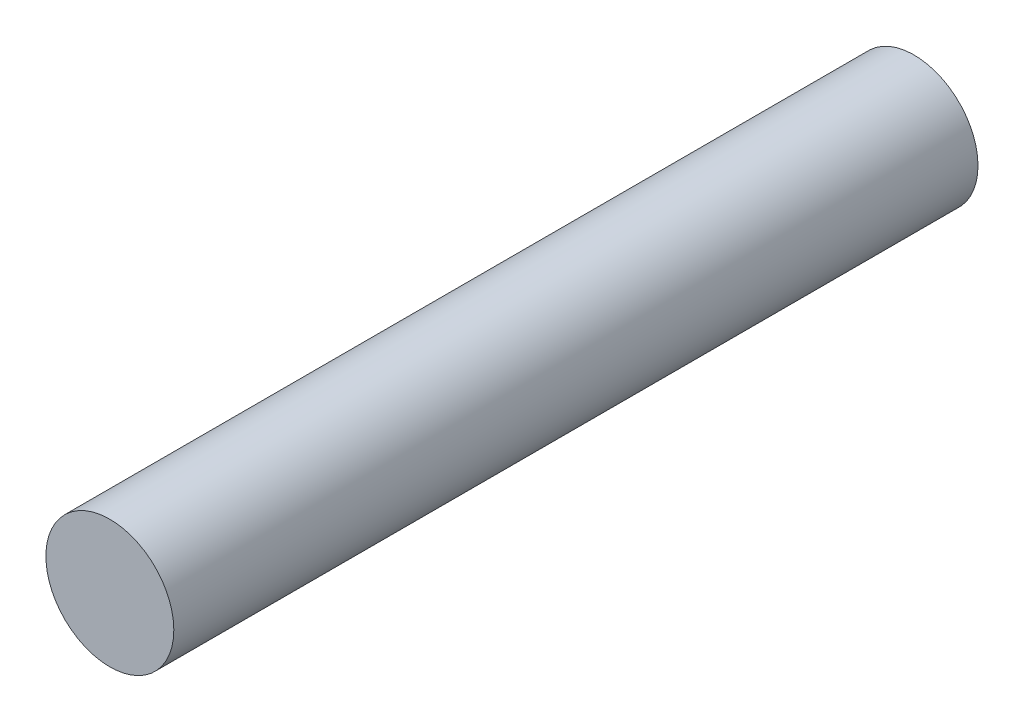
SolidWorks part; units mm, degrees
ref_plane "Top Plane" through (0, 0, 0) normal (0, 0, 1) x (1, 0, 0)
ref_plane "Front Plane" through (0, 0, 0) normal (0, 1, 0) x (1, 0, 0)
ref_plane "Right Plane" through (0, 0, 0) normal (1, 0, 0) x (0, 0, -1)
sketch "Marker Body Sketch" plane through (0, 0, 0) normal (0, 0, 1) x (1, 0, 0)
  circle A0 centre (0, 0) radius 11.1125
  dimension "D1" = 22.225
extrude "Marker Body Extrude" add sketch "Marker Body Sketch" along normal blind 139.7
